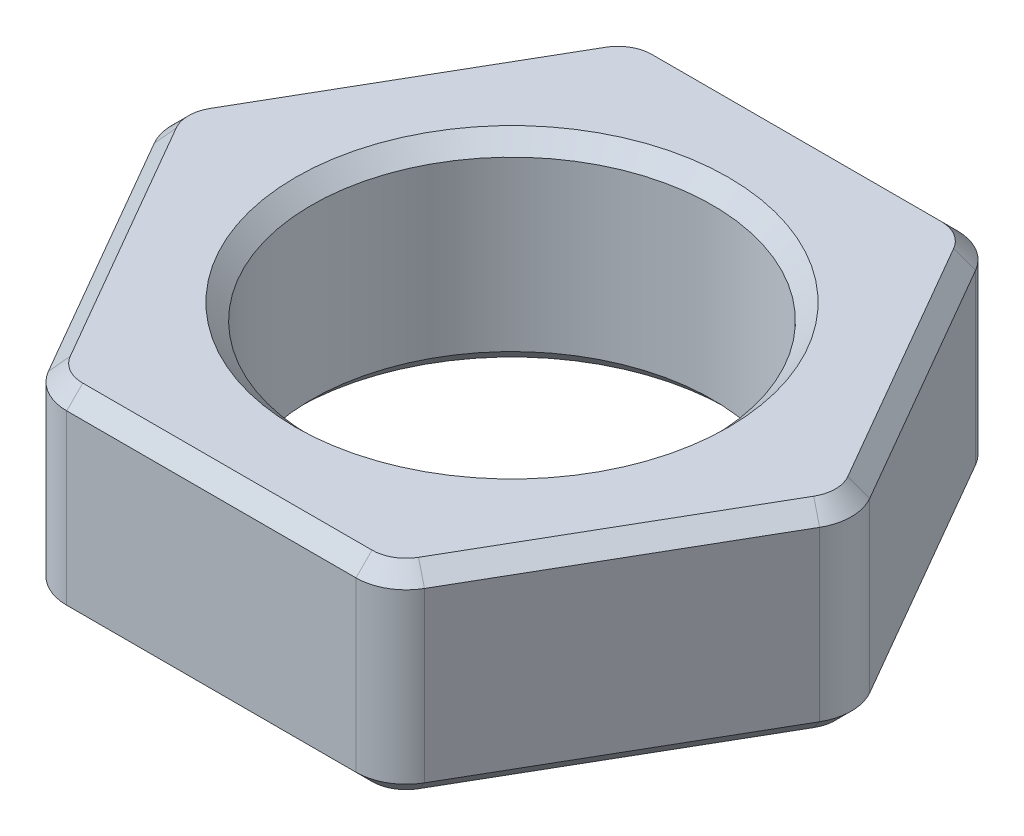
SolidWorks part; units mm, degrees
ref_plane "Front Plane" through (0, 0, 0) normal (0, 0, 1) x (1, 0, 0)
ref_plane "Top Plane" through (0, 0, 0) normal (0, 1, 0) x (1, 0, 0)
ref_plane "Right Plane" through (0, 0, 0) normal (1, 0, 0) x (0, 0, -1)
sketch "Sketch1" plane through (0, 0, 0) normal (0, 1, 0) x (1, 0, 0)
  line L1 (2.7496, 4.7625) -> (-2.7496, 4.7625)
  line L2 (-2.7496, 4.7625) -> (-5.4993, 0)
  line L3 (-5.4993, 0) -> (-2.7496, -4.7625)
  line L4 (-2.7496, -4.7625) -> (2.7496, -4.7625)
  line L5 (2.7496, -4.7625) -> (5.4993, 0)
  line L6 (5.4993, 0) -> (2.7496, 4.7625)
  circle A0 centre (0, 0) radius 3.175
  circle A1 centre (0, 0) radius 4.7625 construction
  point P3 (0, 4.7625)
  dimension "D1" = 6.35
  dimension "D2" = 9.525
extrude "Boss-Extrude1" add sketch "Sketch1" along normal mid plane 3.175
fillet "Fillet1" radius 0.7937 6 edges at (-5.4993, 0, 0) (-2.7496, 0, -4.7625) (2.7496, 0, -4.7625) (5.4993, 0, 0) (-2.7496, 0, 4.7625) (2.7496, 0, 4.7625)
chamfer "Chamfer1" distance 0.254 angle 45 26 edges at (0, -1.5875, 3.175) (-2.6882, -1.5875, 4.6562) (0, -1.5875, 4.7625) (2.6882, -1.5875, 4.6562) (4.1244, -1.5875, 2.3812) (5.3765, -1.5875, 0) (4.1244, -1.5875, -2.3813) (2.6882, -1.5875, -4.6562) (0, -1.5875, -4.7625) (-2.6882, -1.5875, -4.6562) (-4.1244, -1.5875, -2.3812) (-5.3765, -1.5875, 0) (-4.1244, -1.5875, 2.3813) (0, 1.5875, 3.175) (-2.6882, 1.5875, -4.6562) (0, 1.5875, -4.7625) (2.6882, 1.5875, -4.6562) (4.1244, 1.5875, -2.3813) (5.3765, 1.5875, 0) (4.1244, 1.5875, 2.3812) (2.6882, 1.5875, 4.6562) (0, 1.5875, 4.7625) (-2.6882, 1.5875, 4.6562) (-4.1244, 1.5875, 2.3813) (-5.3765, 1.5875, 0) (-4.1244, 1.5875, -2.3812)
